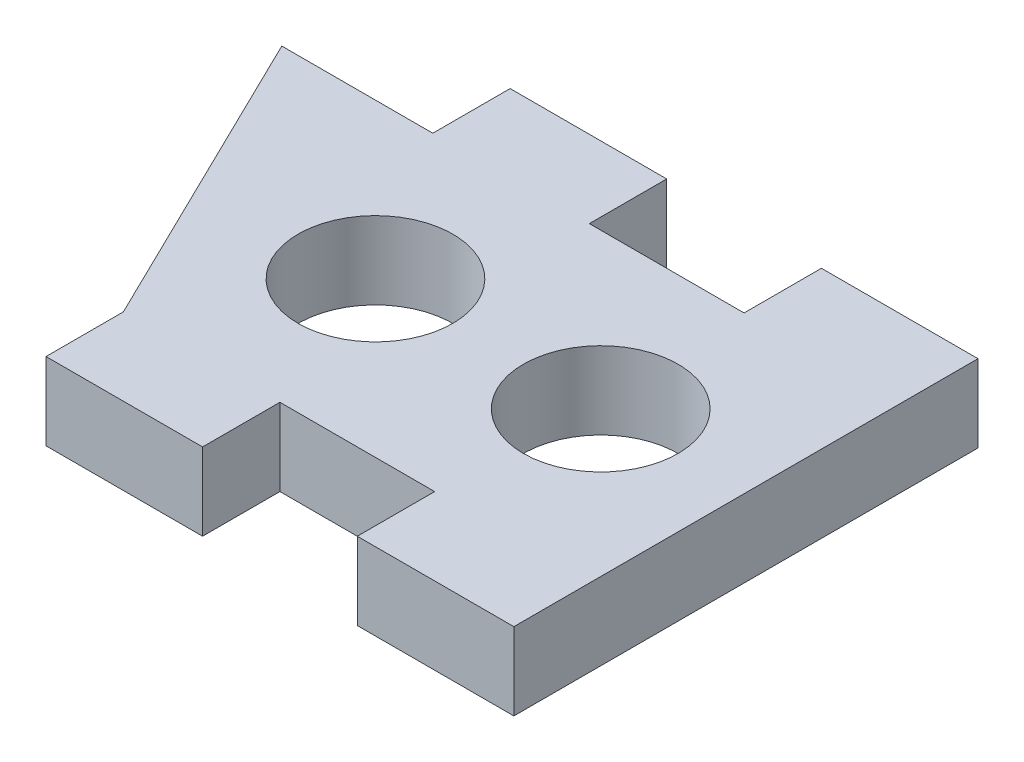
SolidWorks part; units mm, degrees
ref_plane "Front Plane" through (0, 0, 0) normal (0, 0, 1) x (1, 0, 0)
ref_plane "Top Plane" through (0, 0, 0) normal (0, 1, 0) x (1, 0, 0)
ref_plane "Right Plane" through (0, 0, 0) normal (1, 0, 0) x (0, 0, -1)
sketch "Sketch1" plane through (0, 0, 0) normal (0, 1, 0) x (1, 0, 0)
  line L1 (-12.7, 6.35) -> (12.7, 6.35)
  line L2 (-12.7, 6.35) -> (-12.7, -6.35)
  line L3 (-12.7, -6.35) -> (12.7, -6.35)
  line L4 (12.7, 6.35) -> (12.7, -6.35)
  dimension "D1" = 25.4
  dimension "D2" = 12.7
  dimension "D3" = 6.35
  dimension "D4" = 12.7
extrude "Boss-Extrude1" add sketch "Sketch1" along normal blind 3.175
sketch "Sketch2" plane through (0, 0, 6.35) normal (0, 0, 1) x (1, 0, 0)
  line L0 (-12.7, 0) -> (12.7, 0) construction
  line L1 (12.7, 3.175) -> (6.2738, 3.175)
  line L2 (12.7, 3.175) -> (12.7, 0)
  line L3 (12.7, 0) -> (6.2738, 0)
  line L4 (6.2738, 3.175) -> (6.2738, 0)
  line L5 (-12.7, 3.175) -> (12.7, 3.175) construction
  line L6 (-0.0762, 3.175) -> (-6.5024, 3.175)
  line L7 (-0.0762, 3.175) -> (-0.0762, 0)
  line L8 (-0.0762, 0) -> (-6.5024, 0)
  line L9 (-6.5024, 3.175) -> (-6.5024, 0)
  dimension "D1" = 6.4262
  dimension "D2" = 6.4262
  dimension "D3" = 6.35
extrude "Boss-Extrude2" add sketch "Sketch2" along normal blind 3.175
mirror "Mirror1" about plane through (0, 0, 0) normal (0, 0, 1) of "Boss-Extrude2"
sketch "Sketch3" plane through (0, 3.175, 0) normal (0, 1, 0) x (1, 0, 0)
  line L0 (-6.5024, -6.35) -> (-12.7, 6.35)
  line L1 (-12.7, 6.35) -> (-12.7, -6.35)
  line L2 (-12.7, -6.35) -> (-6.5024, -6.35) construction
  line L3 (-12.7, 6.35) -> (-12.7, -6.35) construction
  line L4 (-12.7, -6.35) -> (-6.5024, -6.35)
extrude "Cut-Extrude1" cut sketch "Sketch3" against normal blind 3.175
sketch "Sketch4" plane through (0, 3.175, 0) normal (0, 1, 0) x (1, 0, 0)
  line L0 (-1.7463, 0) -> (1.7463, 0) construction
  circle A0 centre (-2.5059, 0) radius 3.175
  circle A1 centre (6.7413, 0) radius 3.175
  dimension "D1" = 6.35
  dimension "D2" = 6.35
extrude "Cut-Extrude2" cut sketch "Sketch4" against normal through all
